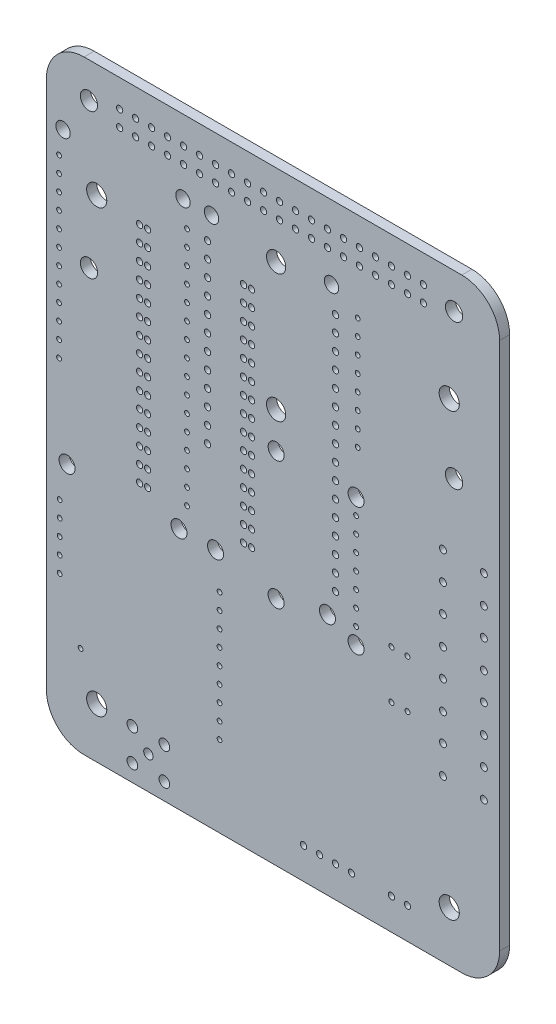
SolidWorks part; units mm, degrees
ref_plane "Front Plane" through (0, 0, 0) normal (0, 0, 1) x (1, 0, 0)
ref_plane "Top Plane" through (0, 0, 0) normal (0, 1, 0) x (1, 0, 0)
ref_plane "Right Plane" through (0, 0, 0) normal (1, 0, 0) x (0, 0, -1)
ref_plane "Plane1" through (0, 0, 1.6) normal (0, 0, 1) x (1, 0, 0)
sketch "Sketch1" plane through (0, 0, 1.6) normal (0, 0, 1) x (1, 0, 0)
  line L0 (35, -118) -> (95, -118)
  line L1 (101, -112) -> (101, -28)
  line L2 (95, -22) -> (35, -22)
  line L3 (29, -28) -> (29, -112)
  circle A0 centre (93.77, -27.62) radius 1.375
  circle A1 centre (88.9, -26.35) radius 0.5
  circle A2 centre (86.36, -26.35) radius 0.5
  circle A3 centre (88.9, -28.89) radius 0.5
  circle A4 centre (86.36, -28.89) radius 0.5
  circle A5 centre (83.82, -26.35) radius 0.5
  circle A6 centre (83.82, -28.89) radius 0.5
  circle A7 centre (93, -40) radius 1.6
  circle A8 centre (81.28, -26.35) radius 0.5
  circle A9 centre (78.74, -26.35) radius 0.5
  circle A10 centre (81.28, -28.89) radius 0.5
  circle A11 centre (78.74, -28.89) radius 0.5
  circle A12 centre (76.2, -26.35) radius 0.5
  circle A13 centre (73.66, -26.35) radius 0.5
  circle A14 centre (76.2, -28.89) radius 0.5
  circle A15 centre (73.66, -28.89) radius 0.5
  circle A16 centre (78.454, -36.195) radius 0.381
  circle A17 centre (74.295, -33.655) radius 1.143
  circle A18 centre (71.12, -26.35) radius 0.5
  circle A19 centre (71.12, -28.89) radius 0.5
  circle A20 centre (68.58, -26.35) radius 0.5
  circle A21 centre (66.04, -26.35) radius 0.5
  circle A22 centre (68.58, -28.89) radius 0.5
  circle A23 centre (66.04, -28.89) radius 0.5
  circle A24 centre (65.5, -34.925) radius 1.524
  circle A25 centre (78.454, -38.735) radius 0.381
  circle A26 centre (78.454, -41.275) radius 0.381
  circle A27 centre (74.93, -37.465) radius 0.5
  circle A28 centre (74.93, -40.005) radius 0.5
  circle A29 centre (74.93, -42.545) radius 0.5
  circle A30 centre (78.454, -43.815) radius 0.381
  circle A31 centre (78.454, -46.355) radius 0.381
  circle A32 centre (74.93, -45.085) radius 0.5
  circle A33 centre (74.93, -47.625) radius 0.5
  circle A34 centre (93.77, -50.62) radius 1.375
  circle A35 centre (98.5, -61.25) radius 0.55
  circle A36 centre (92, -61.25) radius 0.55
  circle A37 centre (98.5, -65.75) radius 0.55
  circle A38 centre (98.5, -70.14) radius 0.55
  circle A39 centre (92, -65.75) radius 0.55
  circle A40 centre (92, -70.14) radius 0.55
  circle A41 centre (78.454, -48.895) radius 0.381
  circle A42 centre (78.454, -51.435) radius 0.381
  circle A43 centre (78.454, -53.975) radius 0.381
  circle A44 centre (74.93, -50.165) radius 0.5
  circle A45 centre (74.93, -52.705) radius 0.5
  circle A46 centre (74.93, -55.245) radius 0.5
  circle A47 centre (74.93, -57.785) radius 0.5
  circle A48 centre (65.5, -55.245) radius 1.524
  circle A49 centre (78.2, -60.96) radius 1.27
  circle A50 centre (78.2, -63.5) radius 0.381
  circle A51 centre (74.93, -60.325) radius 0.5
  circle A52 centre (74.93, -62.865) radius 0.5
  circle A53 centre (78.2, -66.04) radius 0.381
  circle A54 centre (78.2, -68.58) radius 0.381
  circle A55 centre (74.93, -65.405) radius 0.5
  circle A56 centre (74.93, -67.945) radius 0.5
  circle A57 centre (74.93, -70.485) radius 0.5
  circle A58 centre (65.5, -60.96) radius 1.27
  circle A59 centre (63.5, -26.35) radius 0.5
  circle A60 centre (60.96, -26.35) radius 0.5
  circle A61 centre (63.5, -28.89) radius 0.5
  circle A62 centre (60.96, -28.89) radius 0.5
  circle A63 centre (58.42, -26.35) radius 0.5
  circle A64 centre (58.42, -28.89) radius 0.5
  circle A65 centre (55.88, -26.35) radius 0.5
  circle A66 centre (53.34, -26.35) radius 0.5
  circle A67 centre (55.88, -28.89) radius 0.5
  circle A68 centre (53.34, -28.89) radius 0.5
  circle A69 centre (50.8, -26.35) radius 0.5
  circle A70 centre (48.26, -26.35) radius 0.5
  circle A71 centre (50.8, -28.89) radius 0.5
  circle A72 centre (48.26, -28.89) radius 0.5
  circle A73 centre (55.245, -33.655) radius 1.143
  circle A74 centre (50.705, -33.655) radius 1.143
  circle A75 centre (61.595, -40.64) radius 0.5
  circle A76 centre (60.325, -40.64) radius 0.5
  circle A77 centre (61.595, -43.18) radius 0.5
  circle A78 centre (61.595, -45.72) radius 0.5
  circle A79 centre (61.595, -48.26) radius 0.5
  circle A80 centre (60.325, -43.18) radius 0.5
  circle A81 centre (60.325, -45.72) radius 0.5
  circle A82 centre (60.325, -48.26) radius 0.5
  circle A83 centre (54.61, -37.465) radius 0.5
  circle A84 centre (54.61, -40.005) radius 0.5
  circle A85 centre (54.61, -42.545) radius 0.5
  circle A86 centre (51.34, -37.465) radius 0.381
  circle A87 centre (51.34, -40.005) radius 0.381
  circle A88 centre (51.34, -42.545) radius 0.381
  circle A89 centre (54.61, -45.085) radius 0.5
  circle A90 centre (54.61, -47.625) radius 0.5
  circle A91 centre (51.34, -45.085) radius 0.381
  circle A92 centre (51.34, -47.625) radius 0.381
  circle A93 centre (45.72, -26.35) radius 0.5
  circle A94 centre (45.72, -28.89) radius 0.5
  circle A95 centre (43.18, -26.35) radius 0.5
  circle A96 centre (40.64, -26.35) radius 0.5
  circle A97 centre (43.18, -28.89) radius 0.5
  circle A98 centre (40.64, -28.89) radius 0.5
  circle A99 centre (35.77, -27.62) radius 1.375
  circle A100 centre (31.655, -33.655) radius 1.143
  circle A101 centre (45.085, -40.64) radius 0.5
  circle A102 centre (43.815, -40.64) radius 0.5
  circle A103 centre (45.085, -43.18) radius 0.5
  circle A104 centre (43.815, -43.18) radius 0.5
  circle A105 centre (45.085, -45.72) radius 0.5
  circle A106 centre (43.815, -45.72) radius 0.5
  circle A107 centre (45.085, -48.26) radius 0.5
  circle A108 centre (43.815, -48.26) radius 0.5
  circle A109 centre (37, -40) radius 1.6
  circle A110 centre (31.02, -37.465) radius 0.381
  circle A111 centre (31.02, -40.005) radius 0.381
  circle A112 centre (31.02, -42.545) radius 0.381
  circle A113 centre (31.02, -45.085) radius 0.381
  circle A114 centre (31.02, -47.625) radius 0.381
  circle A115 centre (61.595, -50.8) radius 0.5
  circle A116 centre (61.595, -53.34) radius 0.5
  circle A117 centre (60.325, -50.8) radius 0.5
  circle A118 centre (60.325, -53.34) radius 0.5
  circle A119 centre (61.595, -55.88) radius 0.5
  circle A120 centre (61.595, -58.42) radius 0.5
  circle A121 centre (60.325, -55.88) radius 0.5
  circle A122 centre (60.325, -58.42) radius 0.5
  circle A123 centre (54.61, -50.165) radius 0.5
  circle A124 centre (54.61, -52.705) radius 0.5
  circle A125 centre (51.34, -50.165) radius 0.381
  circle A126 centre (51.34, -52.705) radius 0.381
  circle A127 centre (54.61, -55.245) radius 0.5
  circle A128 centre (54.61, -57.785) radius 0.5
  circle A129 centre (51.34, -55.245) radius 0.381
  circle A130 centre (51.34, -57.785) radius 0.381
  circle A131 centre (61.595, -60.96) radius 0.5
  circle A132 centre (61.595, -63.5) radius 0.5
  circle A133 centre (60.325, -60.96) radius 0.5
  circle A134 centre (60.325, -63.5) radius 0.5
  circle A135 centre (61.595, -66.04) radius 0.5
  circle A136 centre (61.595, -68.58) radius 0.5
  circle A137 centre (60.325, -66.04) radius 0.5
  circle A138 centre (60.325, -68.58) radius 0.5
  circle A139 centre (54.61, -60.325) radius 0.5
  circle A140 centre (54.61, -62.865) radius 0.5
  circle A141 centre (51.34, -60.325) radius 0.381
  circle A142 centre (51.34, -62.865) radius 0.381
  circle A143 centre (54.61, -65.405) radius 0.5
  circle A144 centre (51.34, -65.405) radius 0.381
  circle A145 centre (51.34, -67.945) radius 0.381
  circle A146 centre (51.34, -70.485) radius 0.381
  circle A147 centre (45.085, -50.8) radius 0.5
  circle A148 centre (43.815, -50.8) radius 0.5
  circle A149 centre (45.085, -53.34) radius 0.5
  circle A150 centre (43.815, -53.34) radius 0.5
  circle A151 centre (45.085, -55.88) radius 0.5
  circle A152 centre (43.815, -55.88) radius 0.5
  circle A153 centre (45.085, -58.42) radius 0.5
  circle A154 centre (43.815, -58.42) radius 0.5
  circle A155 centre (35.77, -50.62) radius 1.375
  circle A156 centre (31.02, -50.165) radius 0.381
  circle A157 centre (31.02, -52.705) radius 0.381
  circle A158 centre (31.02, -55.245) radius 0.381
  circle A159 centre (31.02, -57.785) radius 0.381
  circle A160 centre (45.085, -60.96) radius 0.5
  circle A161 centre (43.815, -60.96) radius 0.5
  circle A162 centre (45.085, -63.5) radius 0.5
  circle A163 centre (43.815, -63.5) radius 0.5
  circle A164 centre (45.085, -66.04) radius 0.5
  circle A165 centre (43.815, -66.04) radius 0.5
  circle A166 centre (45.085, -68.58) radius 0.5
  circle A167 centre (43.815, -68.58) radius 0.5
  circle A168 centre (31.02, -60.325) radius 0.381
  circle A169 centre (31.02, -62.865) radius 0.381
  circle A170 centre (31.02, -65.405) radius 0.381
  circle A171 centre (98.5, -74.64) radius 0.55
  circle A172 centre (92, -74.64) radius 0.55
  circle A173 centre (98.5, -79.03) radius 0.55
  circle A174 centre (92, -79.03) radius 0.55
  circle A175 centre (86.36, -78.74) radius 0.4
  circle A176 centre (83.82, -78.74) radius 0.4
  circle A177 centre (98.5, -83.53) radius 0.55
  circle A178 centre (98.5, -87.92) radius 0.55
  circle A179 centre (92, -83.53) radius 0.55
  circle A180 centre (92, -87.92) radius 0.55
  circle A181 centre (98.5, -92.42) radius 0.55
  circle A182 centre (92, -92.42) radius 0.55
  circle A183 centre (86.36, -86.36) radius 0.4
  circle A184 centre (83.82, -86.36) radius 0.4
  circle A185 centre (78.2, -71.12) radius 0.381
  circle A186 centre (78.2, -73.66) radius 0.381
  circle A187 centre (78.2, -76.2) radius 0.381
  circle A188 centre (74.93, -73.025) radius 0.5
  circle A189 centre (74.93, -75.565) radius 0.5
  circle A190 centre (78.2, -78.74) radius 0.381
  circle A191 centre (78.2, -81.28) radius 1.27
  circle A192 centre (73.66, -79.375) radius 1.27
  circle A193 centre (65.5, -81.28) radius 1.27
  circle A194 centre (93, -110) radius 1.6
  circle A195 centre (86.36, -113.03) radius 0.5
  circle A196 centre (83.82, -113.03) radius 0.5
  circle A197 centre (77.48, -113.03) radius 0.5
  circle A198 centre (74.94, -113.03) radius 0.5
  circle A199 centre (72.4, -113.03) radius 0.5
  circle A200 centre (69.86, -113.03) radius 0.5
  circle A201 centre (61.595, -71.12) radius 0.5
  circle A202 centre (61.595, -73.66) radius 0.5
  circle A203 centre (61.595, -76.2) radius 0.5
  circle A204 centre (60.325, -71.12) radius 0.5
  circle A205 centre (60.325, -73.66) radius 0.5
  circle A206 centre (60.325, -76.2) radius 0.5
  circle A207 centre (51.34, -73.025) radius 0.381
  circle A208 centre (51.34, -75.565) radius 0.381
  circle A209 centre (55.88, -79.375) radius 1.27
  circle A210 centre (50.07, -79.375) radius 1.27
  circle A211 centre (56.515, -84.836) radius 0.381
  circle A212 centre (56.515, -87.376) radius 0.381
  circle A213 centre (56.515, -89.916) radius 0.381
  circle A214 centre (56.515, -92.456) radius 0.381
  circle A215 centre (45.085, -71.12) radius 0.5
  circle A216 centre (43.815, -71.12) radius 0.5
  circle A217 centre (45.085, -73.66) radius 0.5
  circle A218 centre (43.815, -73.66) radius 0.5
  circle A219 centre (45.085, -76.2) radius 0.5
  circle A220 centre (43.815, -76.2) radius 0.5
  circle A221 centre (32.29, -79.375) radius 1.27
  circle A222 centre (31.115, -84.836) radius 0.381
  circle A223 centre (31.115, -87.376) radius 0.381
  circle A224 centre (31.115, -89.916) radius 0.381
  circle A225 centre (31.115, -92.456) radius 0.381
  circle A226 centre (56.515, -94.996) radius 0.381
  circle A227 centre (56.515, -97.536) radius 0.381
  circle A228 centre (56.515, -100.076) radius 0.381
  circle A229 centre (56.515, -102.616) radius 0.381
  circle A230 centre (56.515, -105.156) radius 0.381
  circle A231 centre (47.752, -110.236) radius 0.85
  circle A232 centre (47.752, -115.316) radius 0.85
  circle A233 centre (31.115, -94.996) radius 0.381
  circle A234 centre (34.445, -103.632) radius 0.381
  circle A235 centre (42.672, -110.236) radius 0.85
  circle A236 centre (45.212, -112.776) radius 0.75
  circle A237 centre (42.672, -115.316) radius 0.85
  circle A238 centre (37, -110) radius 1.6
  arc A239 (29, -112) -> (35, -118) centre (35, -112) ccw
  arc A240 (95, -118) -> (101, -112) centre (95, -112) ccw
  arc A241 (101, -28) -> (95, -22) centre (95, -28) ccw
  arc A242 (35, -22) -> (29, -28) centre (35, -28) ccw
extrude "Boss-Extrude1" add sketch "Sketch1" against normal blind 1.6
